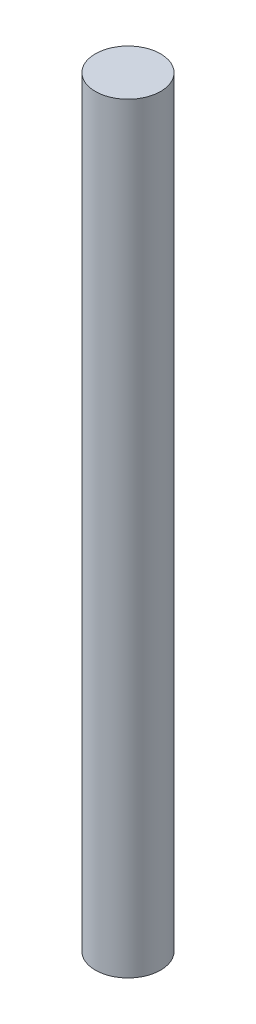
SolidWorks part; units mm, degrees
ref_plane "Face" through (0, 0, 0) normal (0, 0, 1) x (1, 0, 0)
ref_plane "Dessus" through (0, 0, 0) normal (0, 1, 0) x (1, 0, 0)
ref_plane "Droite" through (0, 0, 0) normal (1, 0, 0) x (0, 0, -1)
sketch "Esquisse1" plane through (0, 0, 0) normal (0, 1, 0) x (1, 0, 0)
  circle A0 centre (0, 0) radius 1.5
  dimension "D1" = 3
extrude "Extrusion1" add sketch "Esquisse1" along normal blind 35
